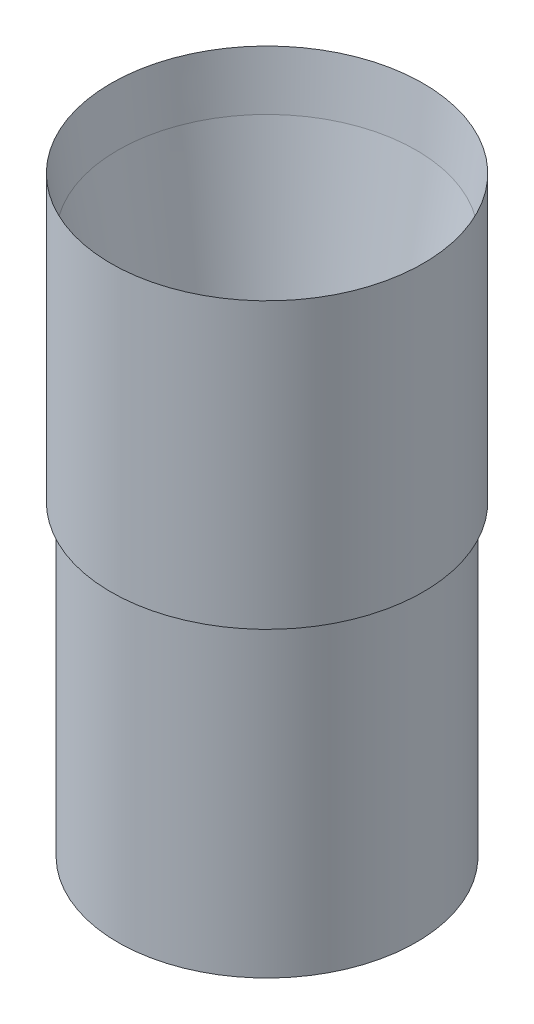
SolidWorks part; units mm, degrees
material "6061-T6 (SS)"
ref_plane "Front Plane" through (0, 0, 0) normal (0, 0, 1) x (1, 0, 0)
ref_plane "Top Plane" through (0, 0, 0) normal (0, 1, 0) x (1, 0, 0)
ref_plane "Right Plane" through (0, 0, 0) normal (1, 0, 0) x (0, 0, -1)
sketch "Sketch1" plane through (0, 0, 0) normal (0, 0, 1) x (1, 0, 0)
  line L13 (2.032, 0) -> (0, 0)
  line L14 (0, 177.8) -> (8.9574, 127)
  line L15 (8.9574, 101.6) -> (2.032, 101.6)
  line L16 (2.032, 101.6) -> (2.032, 0)
  line L18 (0, 177.8) -> (-2.286, 195.8061)
  line L19 (-2.286, 195.8061) -> (-2.286, 101.6)
  line L20 (-2.286, 101.6) -> (0, 101.6)
  line L21 (0, 101.6) -> (0, 0)
  line L22 (49.3903, 245.6415) -> (49.3903, -77.8061) construction
  line L23 (8.9574, 127) -> (8.9574, 101.6)
  dimension "D1" = 80
  dimension "D2" = 50.8
  dimension "D3" = 2.286
  dimension "D4" = 2.032
  dimension "D5" = 101.6
  dimension "D6" = 101.6
  dimension "D7" = 94.2061
  dimension "D8" = 51.6763
revolve "Revolve1" add sketch "Sketch1" angle 360 about L22
